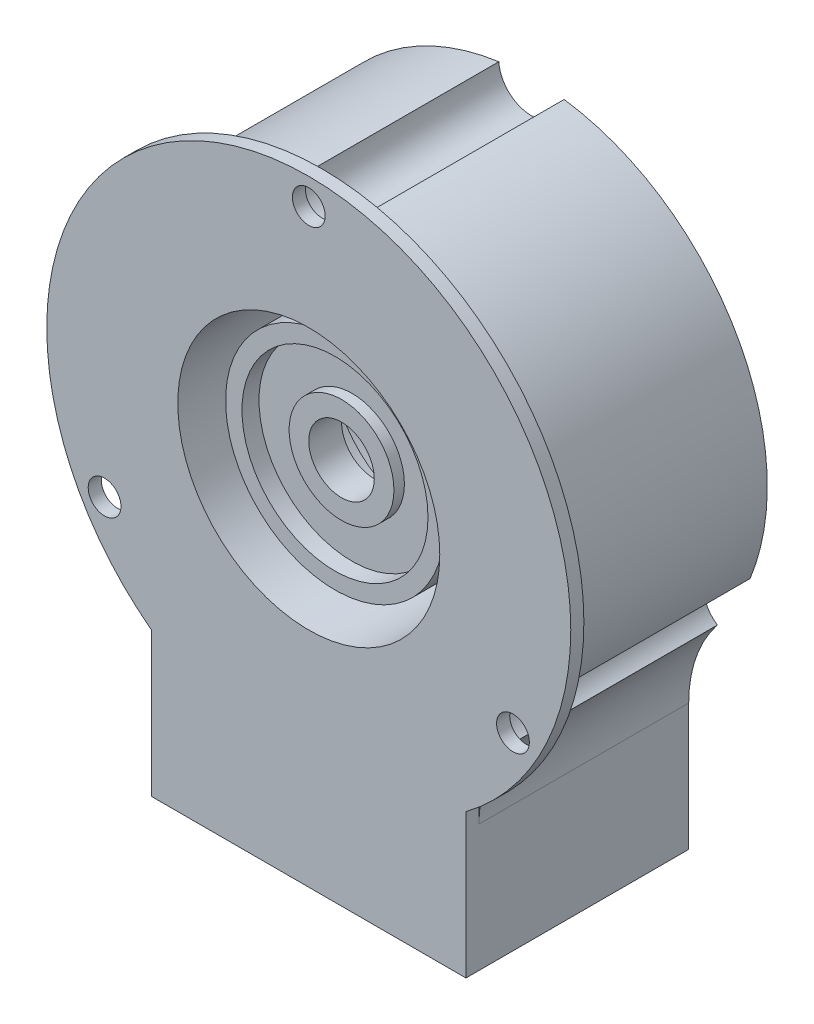
SolidWorks part; units mm, degrees
ref_plane "Front" through (0, 0, 0) normal (0, 0, 1) x (1, 0, 0)
ref_plane "Top" through (0, 0, 0) normal (0, 1, 0) x (1, 0, 0)
ref_plane "Right" through (0, 0, 0) normal (1, 0, 0) x (0, 0, -1)
sketch "Sketch1" plane through (0, 0, 0) normal (0, 0, 1) x (1, 0, 0)
  line L0 (-12, 0) -> (12, 0)
  line L1 (-12, 0) -> (-12, 9.6795)
  line L2 (12, 0) -> (12, 9.6795)
  arc A0 (-14.1429, 15.8654) -> (14.1429, 15.8654) centre (0, 27) cw
  arc A1 (-12, 9.6795) -> (-14.1429, 15.8654) centre (-22, 9.6795) ccw
  arc A2 (12, 9.6795) -> (14.1429, 15.8654) centre (22, 9.6795) cw
  point P2 (0, 0)
  dimension "D2" = 18
  dimension "D4" = 10
  dimension "D1" = 24
  dimension "D3" = 27
extrude "Extrude1" add sketch "Sketch1" along normal blind 16
sketch "Sketch2" plane through (0, 0, 16) normal (0, 0, 1) x (1, 0, 0)
  line L3 (12, 0) -> (12, 9.6795) construction
  line L4 (12, 11) -> (12, 0)
  line L5 (12, 0) -> (-12, 0)
  line L6 (-12, 0) -> (12, 0) construction
  line L7 (-12, 0) -> (-12, 11)
  line L8 (-12, 9.6795) -> (-12, 0) construction
  arc A1 (12, 11) -> (-12, 11) centre (0, 27) ccw
  dimension "D1" = 20
extrude "Extrude2" add sketch "Sketch2" along normal blind 1
hole_wizard "CBORE for M2.5 SHCS1" positions "Sketch5" profile "Sketch4" counterbore size "M2.5" standard "Ansi Metric" end condition through all
sketch "Sketch5" plane through (0, 0, 0) normal (0, 0, -1) x (-1, 0, 0)
  line L0 (0, 27) -> (0, 45) construction
  point P0 (0, 45)
  point P26 (15.5885, 18)
  point P27 (-15.5885, 18)
  dimension "D1" = 18
sketch "Sketch4" plane through (0, 45, 0) normal (1, 0, 0) x (0, 1, 0)
  line L0 (0, 0) -> (0, 17)
  line L1 (0, 17) -> (1.25, 17)
  line L3 (1.25, 17) -> (1.25, 16)
  line L4 (1.25, 16) -> (2.5, 16)
  line L5 (2.5, 16) -> (2.5, 0)
  line L7 (2.5, 0) -> (0, 0)
  line L11 (0, -6.35) -> (0, 107.95) construction
  dimension "Thru Hole Dia." = 2.5
  dimension "Thru Hole Depth" = 17
  dimension "C'Bore Dia." = 5
  dimension "C'Bore Depth" = 16
sketch "Sketch6" plane through (0, 0, 17) normal (0, 0, 1) x (1, 0, 0)
  circle A0 centre (0, 27) radius 10
  dimension "D1" = 20
extrude "Cut-Extrude1" cut sketch "Sketch6" against normal offset from surface (15 mm away) 2 up to face at (0, 18.3648, 0)
ref_axis "Axis1" through (0, 27, 16) along (0, 0, -1)
sketch "Sketch7" plane through (0, 0, 0) normal (1, 0, 0) x (0, 0, -1)
  line L0 (-8, 34.35) -> (-8, 35.35)
  line L1 (-8, 35.35) -> (-15, 35.35)
  line L2 (-15, 35.35) -> (-15, 34.1)
  line L3 (-15, 34.1) -> (-13.7, 34.1)
  line L4 (-13.7, 34.1) -> (-13.7, 31)
  line L5 (-13.7, 31) -> (-14.5, 31)
  line L6 (-14.5, 31) -> (-14.5, 29.5)
  line L7 (-14.5, 29.5) -> (-12, 29.5)
  line L8 (-12, 29.5) -> (-12, 34.35)
  line L9 (-12, 34.35) -> (-8, 34.35)
  line L10 (-16, 27) -> (0, 27) construction
  line L11 (-17, 47) -> (-17, 11) construction
  dimension "D1" = 2.5
  dimension "D2" = 7
  dimension "D3" = 1
  dimension "D4" = 8.35
  dimension "D5" = 1.25
  dimension "D6" = 1.5
  dimension "D7" = 0.5
  dimension "D8" = 1.3
  dimension "D9" = 4
  dimension "D10" = 2
revolve "Revolve1" add sketch "Sketch7" angle 360 about axis through (0, 27, 16) along (0, 0, -1)
